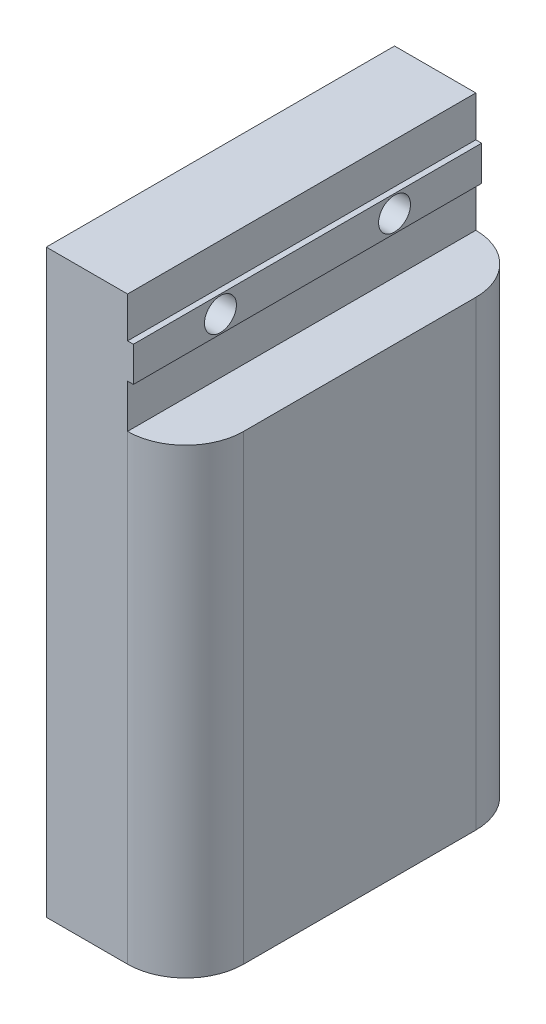
SolidWorks part; units mm, degrees
ref_plane "Alzado" through (0, 0, 0) normal (0, 0, 1) x (1, 0, 0)
ref_plane "Planta" through (0, 0, 0) normal (0, 1, 0) x (1, 0, 0)
ref_plane "Vista lateral" through (0, 0, 0) normal (1, 0, 0) x (0, 0, -1)
sketch "Croquis1" plane through (0, 0, 0) normal (0, 0, 1) x (1, 0, 0)
  line L4 (24, -100) -> (24, -20.5)
  line L5 (24, -20.5) -> (14, -20.5)
  line L6 (14, -20.5) -> (14, 0)
  line L7 (14, 0) -> (0, 0)
  line L8 (0, 0) -> (0, -100)
  line L9 (0, -100) -> (24, -100)
  dimension "D1" = 14
  dimension "D2" = 100
  dimension "D3" = 10
  dimension "D4" = 20.5
extrude "Saliente-Extruir1" add sketch "Croquis1" along normal blind 60
sketch "Croquis4" plane through (14, 0, 0) normal (1, 0, 0) x (0, 0, -1)
  line L0 (-60, -20.5) -> (-60, 0) construction
  line L1 (-60, -7) -> (0, -7)
  line L2 (-60, -7) -> (-60, -13)
  line L3 (-60, -13) -> (0, -13)
  line L4 (0, -7) -> (0, -13)
  line L5 (0, -20.5) -> (0, 0) construction
  line L6 (-60, 0) -> (0, 0) construction
  point P8 (-60, -10)
  dimension "D1" = 6
  dimension "D2" = 10
extrude "Saliente-Extruir3" add sketch "Croquis4" along normal blind 1
sketch "Croquis5" plane through (0, 0, 0) normal (-1, 0, 0) x (0, 0, 1)
  line L0 (60, 0) -> (0, 0) construction
  circle A0 centre (15, -10) radius 2.75
  circle A1 centre (45, -10) radius 2.75
  dimension "D1" = 5.5
  dimension "D2" = 5.5
  dimension "D3" = 30
  dimension "D4" = 15
  dimension "D5" = 10
  dimension "D6" = 10
extrude "Cortar-Extruir1" cut sketch "Croquis5" against normal through all
sketch "Croquis6" plane through (0, 0, 0) normal (-1, 0, 0) x (0, 0, 1)
  circle A0 centre (15, -10) radius 6
  circle A1 centre (45, -10) radius 6
  dimension "D1" = 12
  dimension "D2" = 12
extrude "Cortar-Extruir2" cut sketch "Croquis6" against normal blind 8
fillet "Redondeo1" radius 10 2 edges at (24, -60.25, 0) (24, -60.25, 60)
